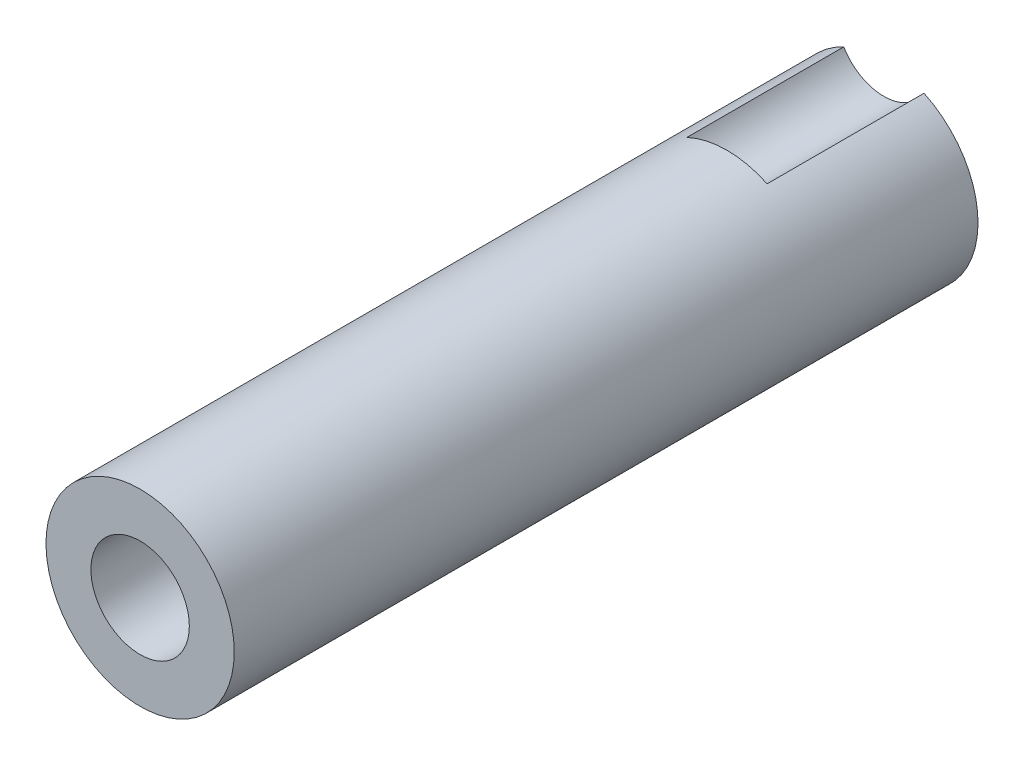
SolidWorks part; units mm, degrees
ref_plane "Front Plane" through (0, 0, 0) normal (0, 0, 1) x (1, 0, 0)
ref_plane "Top Plane" through (0, 0, 0) normal (0, 1, 0) x (1, 0, 0)
ref_plane "Right Plane" through (0, 0, 0) normal (1, 0, 0) x (0, 0, -1)
sketch "Sketch1" plane through (0, 0, 0) normal (0, 0, 1) x (1, 0, 0)
  circle A0 centre (0, 0) radius 12.5349
  dimension "D1" = 25.0698
extrude "Boss-Extrude1" add sketch "Sketch1" along normal blind 6.4389
sketch "Sketch2" plane through (0, 0, 6.4389) normal (0, 0, 1) x (1, 0, 0)
  line L0 (-9.8298, 7.7781) -> (9.8298, 7.7781)
  circle A0 centre (0, 0) radius 12.5349 construction
  arc A1 (-9.8298, 7.7781) -> (9.8298, 7.7781) centre (0, 0) cw
  dimension "D1" = 19.6596
extrude "Boss-Extrude2" add sketch "Sketch2" along normal blind 4.0386
sketch "Sketch3" plane through (0, 0, 6.4389) normal (0, 0, 1) x (1, 0, 0)
  circle A0 centre (0, 0) radius 6.4008
  dimension "D1" = 12.8016
extrude "Boss-Extrude3" add sketch "Sketch3" along normal blind 44.1325
sketch "Sketch4" plane through (0, 0, 0) normal (0, 0, -1) x (-1, 0, 0)
  line L0 (0, -2.2629) -> (0, 10.8919) construction
  circle A0 centre (0, 7.4104) radius 3.175
  circle A1 centre (0, 0) radius 12.5349 construction
  dimension "D1" = 6.35
  dimension "D2" = 7.4104
extrude "Cut-Extrude1" cut sketch "Sketch4" against normal blind 10.668
sketch "Sketch5" plane through (0, 0, 0) normal (0, 0, -1) x (-1, 0, 0)
  line L0 (2.667, -12.2479) -> (-2.667, -12.2479)
  circle A0 centre (0, 0) radius 12.5349 construction
  arc A1 (-2.667, -12.2479) -> (2.667, -12.2479) centre (0, 0) ccw
  dimension "D1" = 5.334
extrude "Cut-Extrude2" cut sketch "Sketch5" against normal through all
sketch "Sketch6" plane through (0, 0, 50.5714) normal (0, 0, 1) x (1, 0, 0)
  circle A0 centre (0, 0) radius 3.3464
  dimension "D1" = 6.6929
extrude "Cut-Extrude3" cut sketch "Sketch6" against normal through all
sketch "Sketch7" plane through (0, 0, 0) normal (0, 0, -1) x (-1, 0, 0)
  circle A0 centre (0, 0) radius 6.4008
  circle A1 centre (0, 0) radius 12.5349
  dimension "D1" = 12.8016
  dimension "D2" = 25.0698
extrude "Cut-Extrude4" cut sketch "Sketch7" against normal through all
sketch "Sketch9" plane through (0, 0, 0) normal (0, 0, 1) x (1, 0, 0)
  line L0 (0, -6.4008) -> (6.4008, -6.4008) construction
sketch "Sketch10" plane through (0, 0, 50.5714) normal (0, 0, 1) x (1, 0, 0)
  line L0 (0.307, -6.4008) -> (-8.2919, -6.4008) construction
sketch3d "3DSketch1"
  line L0 (0.307, -6.4008, 50.5714) -> (-8.2919, -6.4008, 50.5714) construction
  line L1 (0, -6.4008, 0) -> (6.4008, -6.4008, 0) construction
sketch "Sketch11" plane through (0, -6.4008, 0) normal (0, 1, 0) x (-1, 0, 0)
  circle A0 centre (0, 42.0697) radius 0.8484
extrude "Cut-Extrude5" cut sketch "Sketch11" along normal blind 5.08
